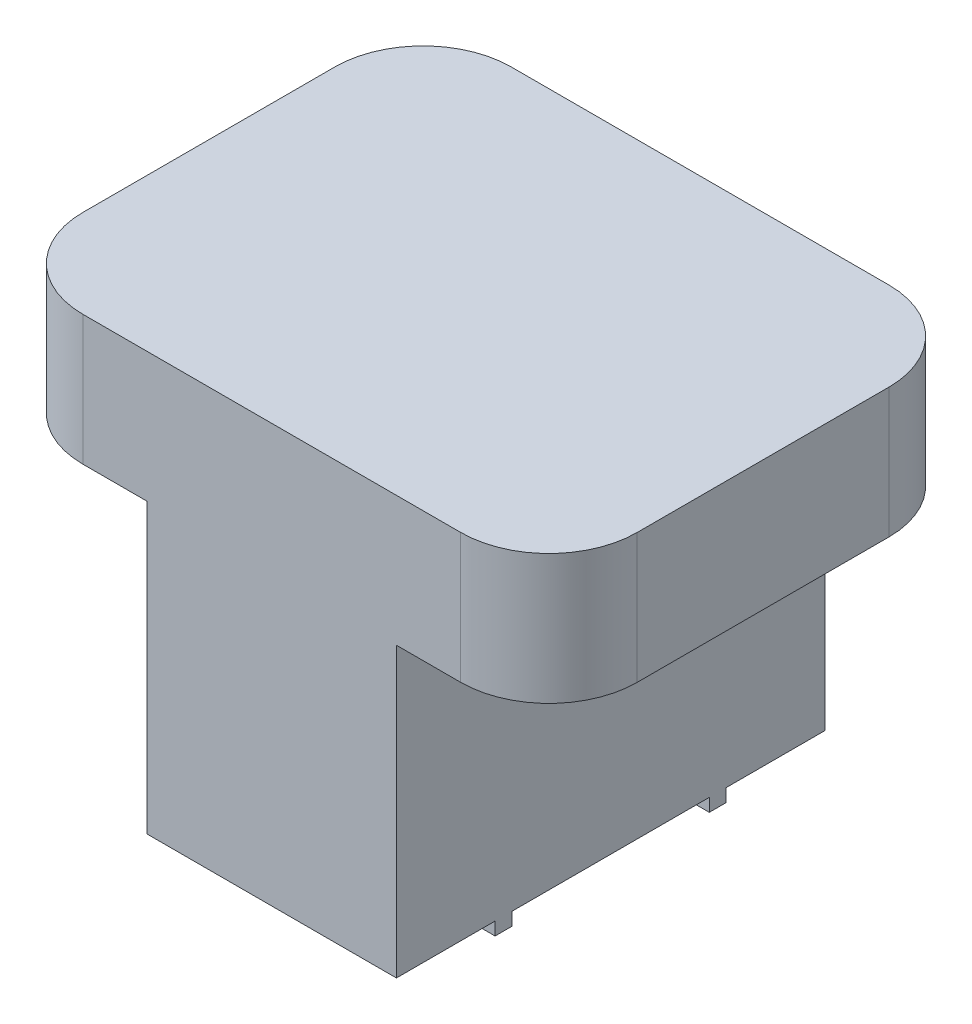
SolidWorks part; units mm, degrees
ref_plane "YZ" through (0, 0, 0) normal (0, 0, 1) x (1, 0, 0)
ref_plane "XY" through (0, 0, 0) normal (0, 1, 0) x (1, 0, 0)
ref_plane "XZ" through (0, 0, 0) normal (1, 0, 0) x (0, 0, -1)
sketch "Sketch1" plane through (0, 0, 0) normal (0, 1, 0) x (1, 0, 0)
  line L0 (-18.4785, 20.955) -> (18.4785, 20.955)
  line L1 (-27.1145, 12.319) -> (-27.1145, -12.319)
  line L2 (18.4785, -20.955) -> (-18.4785, -20.955)
  line L3 (27.1145, -12.319) -> (27.1145, 12.319)
  line L4 (27.1145, 0) -> (0, 0) construction
  line L5 (0, 20.955) -> (0, 0) construction
  arc A0 (27.1145, 12.319) -> (18.4785, 20.955) centre (18.4785, 12.319) ccw
  arc A1 (-27.1145, 12.319) -> (-18.4785, 20.955) centre (-18.4785, 12.319) cw
  arc A2 (-27.1145, -12.319) -> (-18.4785, -20.955) centre (-18.4785, -12.319) ccw
  arc A3 (27.1145, -12.319) -> (18.4785, -20.955) centre (18.4785, -12.319) cw
  dimension "D3" = 8.636
  dimension "D4" = 8.636
  dimension "D5" = 8.636
  dimension "D6" = 8.636
  dimension "D1" = 54.229
  dimension "D2" = 41.91
extrude "Base-Extrude" add sketch "Sketch1" along normal mid plane 40.894
sketch "Sketch2" plane through (0, -20.447, 0) normal (0, -1, 0) x (1, 0, 0)
  line L0 (12.192, -20.955) -> (18.4785, -20.955)
  line L1 (12.192, 20.955) -> (12.192, -20.955)
  line L2 (-12.192, 20.955) -> (-18.4785, 20.955)
  line L3 (-12.192, -20.955) -> (-12.192, 20.955)
  line L4 (18.4785, 20.955) -> (-18.4785, 20.955) construction
  line L5 (-18.4785, -20.955) -> (18.4785, -20.955) construction
  line L6 (12.192, 0) -> (-12.192, 0) construction
  line L9 (27.1145, -12.319) -> (27.1145, 12.319)
  line L10 (18.4785, 20.955) -> (-18.4785, 20.955)
  line L11 (-27.1145, 12.319) -> (-27.1145, -12.319)
  line L12 (-18.4785, -20.955) -> (18.4785, -20.955)
  line L13 (27.1145, -12.319) -> (27.1145, 12.319)
  line L14 (18.4785, 20.955) -> (12.192, 20.955)
  line L15 (-27.1145, 12.319) -> (-27.1145, -12.319)
  line L16 (-18.4785, -20.955) -> (-12.192, -20.955)
  arc A4 (18.4785, -20.955) -> (27.1145, -12.319) centre (18.4785, -12.319) ccw
  arc A5 (27.1145, 12.319) -> (18.4785, 20.955) centre (18.4785, 12.319) ccw
  arc A6 (-18.4785, 20.955) -> (-27.1145, 12.319) centre (-18.4785, 12.319) ccw
  arc A7 (-27.1145, -12.319) -> (-18.4785, -20.955) centre (-18.4785, -12.319) ccw
  arc A8 (18.4785, -20.955) -> (27.1145, -12.319) centre (18.4785, -12.319) ccw
  arc A9 (27.1145, 12.319) -> (18.4785, 20.955) centre (18.4785, 12.319) ccw
  arc A10 (-18.4785, 20.955) -> (-27.1145, 12.319) centre (-18.4785, 12.319) ccw
  arc A11 (-27.1145, -12.319) -> (-18.4785, -20.955) centre (-18.4785, -12.319) ccw
  dimension "D1" = 24.384
  dimension "D2" = 0
extrude "Cut-Extrude1" cut sketch "Sketch2" against normal offset from surface (28.194 mm away) 12.7
sketch "Sketch3" plane through (0, -20.447, 0) normal (0, -1, 0) x (1, 0, 0)
  line L0 (12.192, -9.652) -> (6.7056, -9.652)
  line L1 (12.192, -9.652) -> (12.192, -11.303)
  line L2 (6.7056, -11.303) -> (12.192, -11.303)
  line L3 (6.7056, -11.303) -> (6.7056, -9.652)
  line L4 (12.192, 20.955) -> (12.192, -20.955) construction
  line L5 (12.192, 11.303) -> (6.7056, 11.303)
  line L6 (12.192, 11.303) -> (12.192, 9.652)
  line L7 (6.7056, 9.652) -> (12.192, 9.652)
  line L8 (6.7056, 9.652) -> (6.7056, 11.303)
  line L9 (-6.7056, 11.303) -> (-12.192, 11.303)
  line L10 (-6.7056, 11.303) -> (-6.7056, 9.652)
  line L11 (-12.192, 9.652) -> (-6.7056, 9.652)
  line L12 (-12.192, 9.652) -> (-12.192, 11.303)
  line L13 (-12.192, -20.955) -> (-12.192, 20.955) construction
  line L14 (-6.7056, -9.652) -> (-12.192, -9.652)
  line L15 (-6.7056, -9.652) -> (-6.7056, -11.303)
  line L16 (-12.192, -11.303) -> (-6.7056, -11.303)
  line L17 (-12.192, -11.303) -> (-12.192, -9.652)
  line L18 (6.7056, 11.303) -> (6.7056, 20.955) construction
  line L19 (12.192, 20.955) -> (-12.192, 20.955) construction
  line L20 (6.7056, -11.303) -> (6.7056, -20.955) construction
  line L21 (-12.192, -20.955) -> (12.192, -20.955) construction
  dimension "D1" = 5.4864
  dimension "D2" = 1.651
  dimension "D3" = 22.606
extrude "Boss-Extrude1" add sketch "Sketch3" along normal blind 1.27
